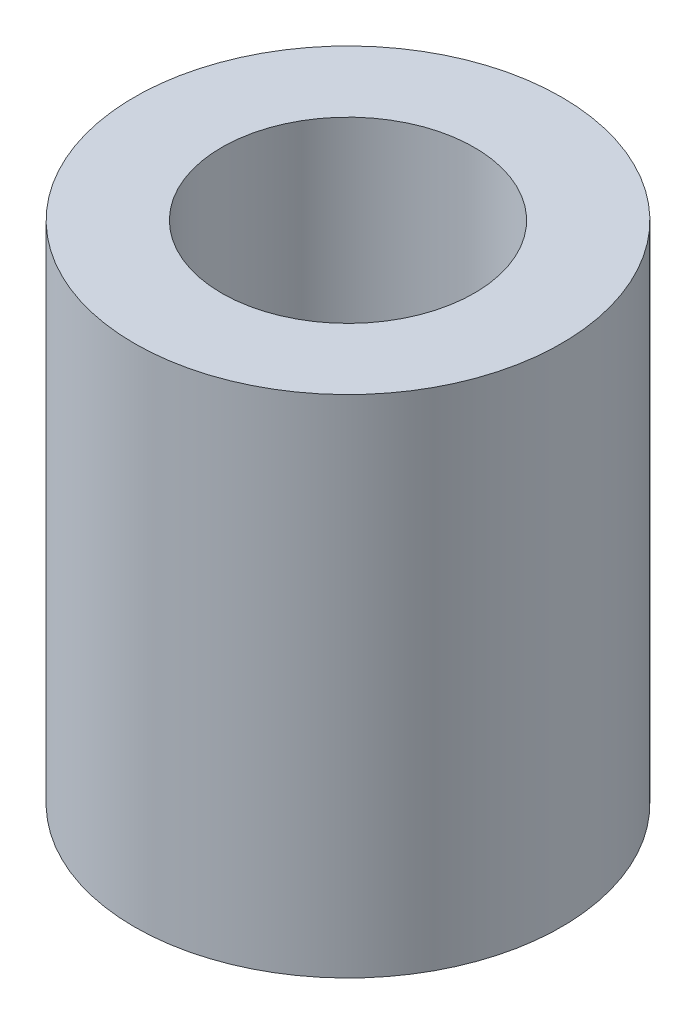
SolidWorks part; units mm, degrees
ref_plane "Front Plane" through (0, 0, 0) normal (0, 0, 1) x (1, 0, 0)
ref_plane "Top Plane" through (0, 0, 0) normal (0, 1, 0) x (1, 0, 0)
ref_plane "Right Plane" through (0, 0, 0) normal (1, 0, 0) x (0, 0, -1)
sketch "Sketch1" plane through (0, 0, 0) normal (0, 1, 0) x (1, 0, 0)
  circle A0 centre (0, 0) radius 6.35
  circle A1 centre (0, 0) radius 10.7315
  dimension "D1" = 12.7
  dimension "D2" = 21.463
extrude "Boss-Extrude1" add sketch "Sketch1" along normal mid plane 25.4 contours A1 | A0
